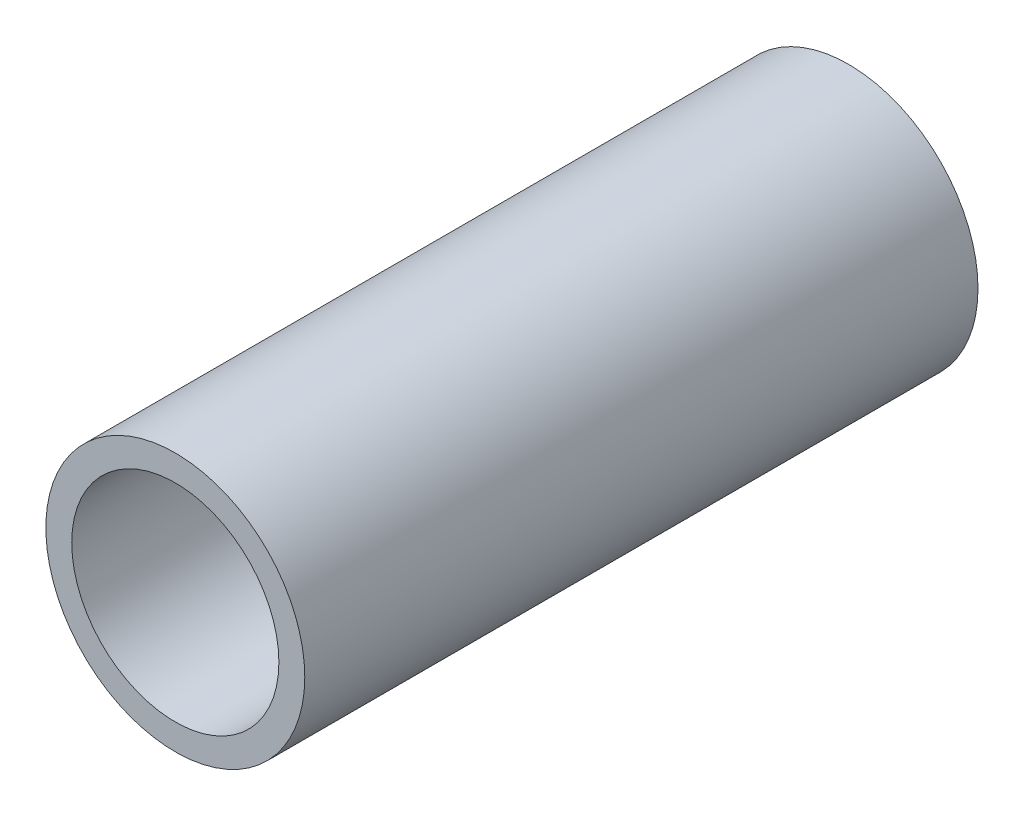
SolidWorks part; units mm, degrees
material "6061-T6 (SS)"
ref_plane "Front Plane" through (0, 0, 0) normal (0, 0, 1) x (1, 0, 0)
ref_plane "Top Plane" through (0, 0, 0) normal (0, 1, 0) x (1, 0, 0)
ref_plane "Right Plane" through (0, 0, 0) normal (1, 0, 0) x (0, 0, -1)
sketch "Sketch1" plane through (0, 0, 0) normal (0, 0, 1) x (1, 0, 0)
  circle A0 centre (0, 0) radius 2.5
  dimension "D1" = 5
extrude "Boss-Extrude1" add sketch "Sketch1" along normal blind 13
sketch "Sketch2" plane through (0, 0, 13) normal (0, 0, 1) x (1, 0, 0)
  circle A0 centre (0, 0) radius 2
  dimension "D1" = 4
extrude "Cut-Extrude1" cut sketch "Sketch2" against normal through all
